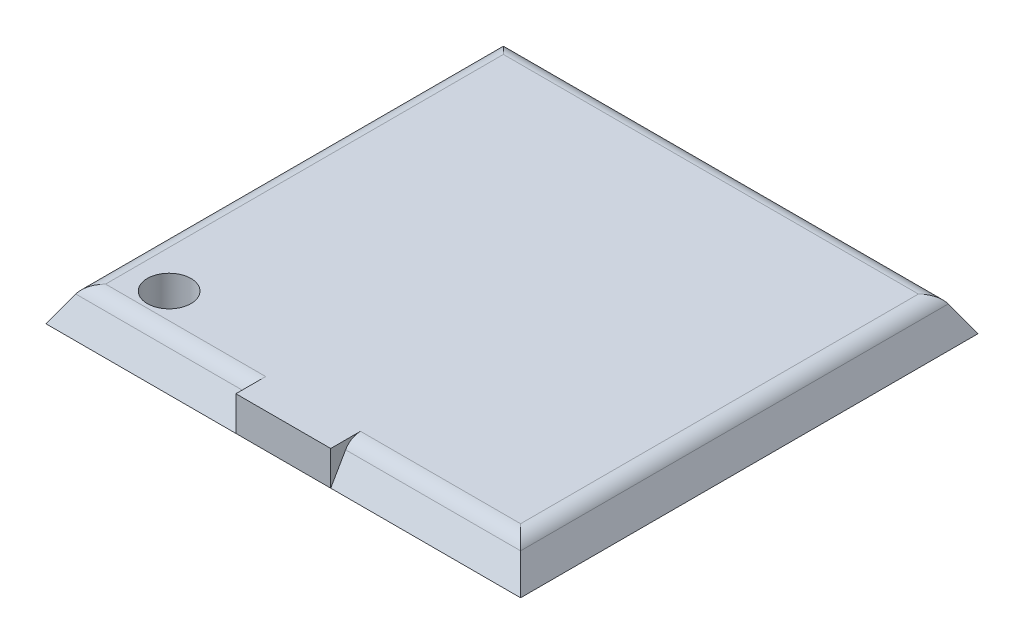
SolidWorks part; units mm, degrees
ref_plane "Front Plane" through (0, 0, 0) normal (0, 0, 1) x (1, 0, 0)
ref_plane "Top Plane" through (0, 0, 0) normal (0, 1, 0) x (1, 0, 0)
ref_plane "Right Plane" through (0, 0, 0) normal (1, 0, 0) x (0, 0, -1)
sketch "Sketch1" plane through (0, 0, 0) normal (0, 1, 0) x (1, 0, 0)
  line L1 (-13.8, 13.3) -> (13.8, 13.3)
  line L2 (-13.8, 13.3) -> (-13.8, -13.3)
  line L3 (-13.8, -13.3) -> (13.8, -13.3)
  line L4 (13.8, 13.3) -> (13.8, -13.3)
  line L5 (-13.8, 13.3) -> (13.8, -13.3) construction
  line L6 (-13.8, -13.3) -> (13.8, 13.3) construction
  point P0 (0, 0)
  dimension "D1" = 27.6
  dimension "D2" = 26.6
extrude "Boss-Extrude1" add sketch "Sketch1" along normal blind 2 draft 30
sketch "Sketch2" plane through (0, 0, 0) normal (0, 0, 1) x (1, 0, 0)
  line L0 (-13.8, 0) -> (13.8, 0) construction
  line L1 (-2.7573, 0) -> (2.7573, 0)
  line L2 (-2.7573, 0) -> (-2.7573, 2)
  line L3 (-2.7573, 2) -> (2.7573, 2)
  line L4 (2.7573, 0) -> (2.7573, 2)
  line L5 (-12.6453, 2) -> (12.6453, 2) construction
  line L6 (0, 0) -> (0, 4.9816) construction
extrude "Boss-Extrude2" add sketch "Sketch2" along normal blind 13.3
sketch "Sketch3" plane through (0, 0, 0) normal (0, 1, 0) x (1, 0, 0)
  line L1 (-13.8, -13.3) -> (-2.7573, -13.3) construction
  line L3 (-13.8, 13.3) -> (-13.8, -13.3) construction
  circle A0 centre (-9.87, -10.07) radius 1.27
  point P2 (-9.87, -11.34)
  point P7 (-11.14, -10.07)
  dimension "D1" = 1.96
  dimension "D2" = 2.66
  dimension "D3" = 2.54
extrude "Cut-Extrude1" cut sketch "Sketch3" along normal through all
fillet "Fillet5" radius 1 5 edges at (0, 2, -12.1453) (12.6453, 2, 0) (7.7013, 2, 12.1453) (-7.7013, 2, 12.1453) (-12.6453, 2, 0)
